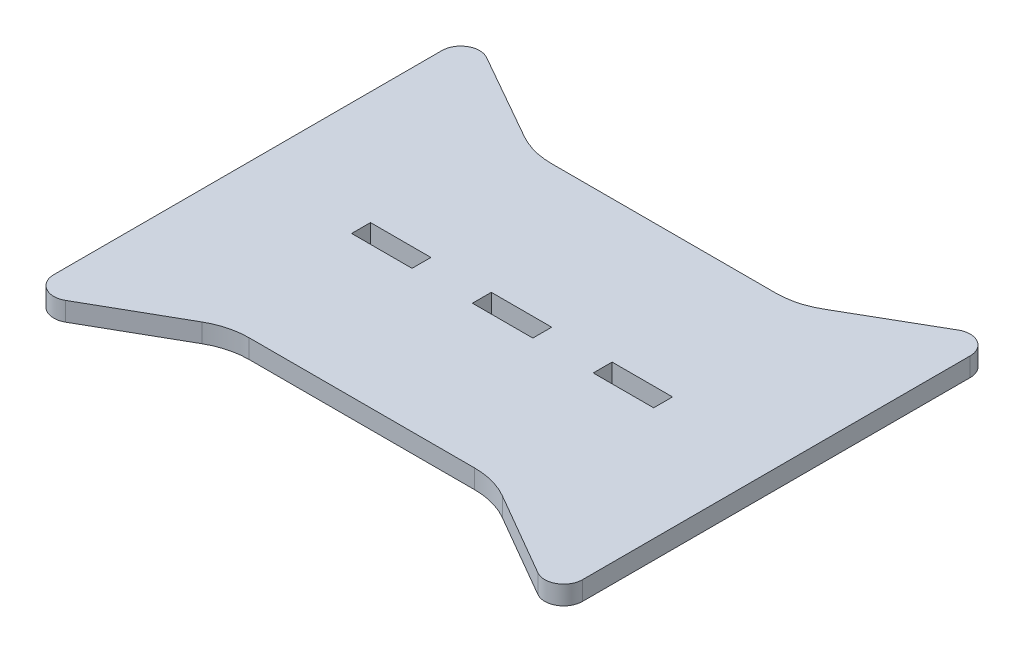
SolidWorks part; units mm, degrees
ref_plane "Front Plane" through (0, 0, 0) normal (0, 0, 1) x (1, 0, 0)
ref_plane "Top Plane" through (0, 0, 0) normal (0, 1, 0) x (1, 0, 0)
ref_plane "Right Plane" through (0, 0, 0) normal (1, 0, 0) x (0, 0, -1)
sketch "Sketch1" plane through (0, 0, 0) normal (0, 1, 0) x (1, 0, 0)
  line L5 (-8, 2.5) -> (8, 2.5)
  line L7 (-40, 2.5) -> (-24, 2.5)
  line L8 (-40, 2.5) -> (-40, -2.5)
  line L9 (-40, -2.5) -> (-24, -2.5)
  line L10 (40, 2.5) -> (40, -2.5)
  line L11 (24, 2.5) -> (40, 2.5)
  line L12 (-24, 2.5) -> (-24, -2.5)
  line L13 (-8, 2.5) -> (-8, -2.5)
  line L14 (8, 2.5) -> (8, -2.5)
  line L15 (24, 2.5) -> (24, -2.5)
  line L16 (-8, -2.5) -> (8, -2.5)
  line L17 (24, -2.5) -> (40, -2.5)
  line L18 (-29.4954, 40) -> (29.8796, 40)
  line L20 (-70, 51.4111) -> (-70, -51.3935)
  line L22 (70, 51.357) -> (70, -51.3288)
  line L23 (-70, 60) -> (70, -60) construction
  line L24 (-70, -60) -> (70, 60) construction
  line L25 (-29.6217, -40) -> (30.0759, -40)
  line L26 (62.5075, 55.6915) -> (39.8496, 42.6622)
  line L27 (-62.5311, 55.759) -> (-39.3708, 42.6082)
  line L28 (62.4952, -55.6561) -> (40.0949, -42.6905)
  line L29 (-62.5234, -55.7371) -> (-39.5281, -42.6257)
  arc A0 (-29.4954, 40) -> (-39.3708, 42.6082) centre (-29.4954, 60) cw
  arc A1 (29.8796, 40) -> (39.8496, 42.6622) centre (29.8796, 60) ccw
  arc A2 (-39.5281, -42.6257) -> (-29.6217, -40) centre (-29.6217, -60) cw
  arc A3 (30.0759, -40) -> (40.0949, -42.6905) centre (30.0759, -60) cw
  arc A4 (-70, 51.4111) -> (-62.5311, 55.759) centre (-65, 51.4111) cw
  arc A5 (62.5075, 55.6915) -> (70, 51.357) centre (65, 51.357) cw
  arc A6 (62.4952, -55.6561) -> (70, -51.3288) centre (65, -51.3288) ccw
  arc A7 (-70, -51.3935) -> (-62.5234, -55.7371) centre (-65, -51.3935) ccw
  point P0 (0, 0)
  point P1 (0, 0)
  point P18 (0, 0)
  dimension "D3" = 20
  dimension "D4" = 20
  dimension "D5" = 20
  dimension "D6" = 20
  dimension "D1" = 140
  dimension "D9" = 5
  dimension "D10" = 5
  dimension "D11" = 5
  dimension "D12" = 5
  dimension "D2" = 120
  dimension "D7" = 80
  dimension "D8" = 5
extrude "Boss-Extrude1" add sketch "Sketch1" along normal blind 5
